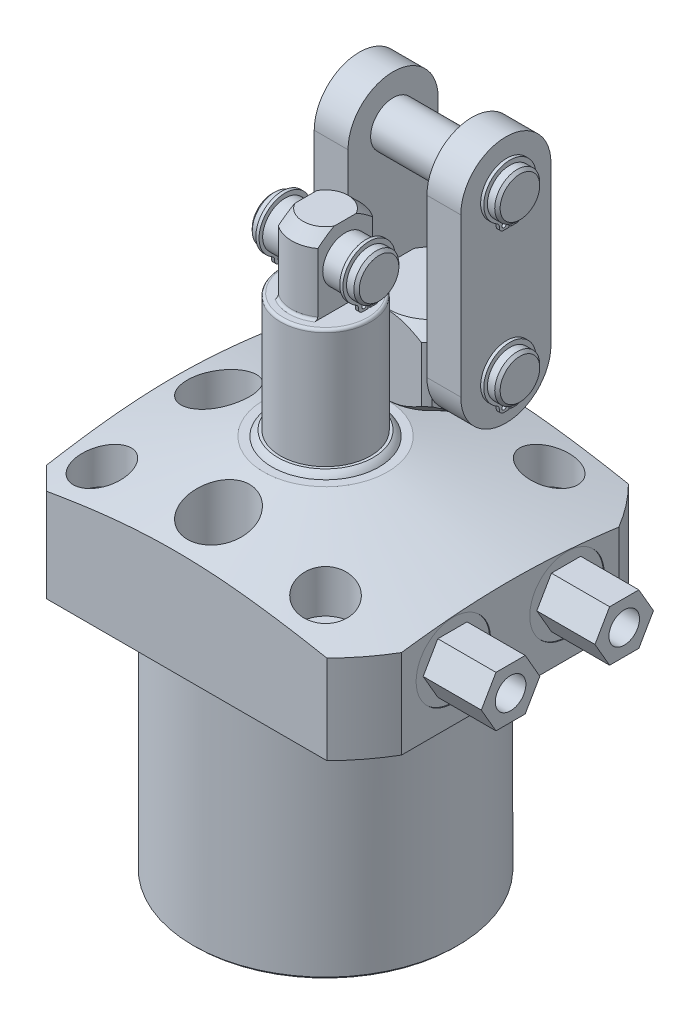
SolidWorks part; units mm, degrees
material "Alloy Steel"
ref_plane "Front Plane" through (0, 0, 0) normal (0, 0, 1) x (1, 0, 0)
ref_plane "Top Plane" through (0, 0, 0) normal (0, 1, 0) x (1, 0, 0)
ref_plane "Right Plane" through (0, 0, 0) normal (1, 0, 0) x (0, 0, -1)
sketch "Sketch28" plane through (0, 0, 0) normal (0, 0, 1) x (1, 0, 0)
  line L0 (0, 0) -> (0, 146.1857) construction
  line L1 (-17.4625, 36.4998) -> (-60.325, 25.0148)
  line L2 (-60.325, 25.0148) -> (-60.325, 0)
  line L3 (-60.325, 0) -> (-37.2999, 0)
  line L6 (-37.2999, 0) -> (-37.2999, -69.85)
  line L9 (-37.2999, -69.85) -> (0, -69.85)
  line L10 (0, -69.85) -> (0, 36.4998)
  line L11 (0, 36.4998) -> (-17.4625, 36.4998)
  dimension "D2" = 74.5998
  dimension "D3" = 69.85
  dimension "D5" = 120.65
  dimension "D6" = 15
  dimension "D7" = 34.925
  dimension "D8" = 36.4998
revolve "Revolve7" add sketch "Sketch28" angle 360 about L0
sketch "Sketch3" plane through (0, 36.4998, 0) normal (0, 1, 0) x (-1, 0, 0)
  line L0 (42.4688, -42.4688) -> (-51.9938, -42.4688)
  line L3 (-51.9938, 42.4688) -> (42.4688, 42.4688)
  line L4 (42.4688, -42.4688) -> (42.4688, 42.4688)
  line L5 (-51.9938, -42.4688) -> (-51.9938, 42.4688)
  line L6 (-29.7523, 0) -> (31.3525, 0) construction
  dimension "D1" = 84.9376
  dimension "D2" = 51.9938
  dimension "D5" = 42.4688
extrude "Cut-Extrude9" cut sketch "Sketch3" against normal up to next (106.3498 mm away) flip side to cut
chamfer "Chamfer8" distance 6.35 angle 45 2 edges at (-42.4688, 12.5429, -42.4688) (-42.4688, 12.5429, 42.4688)
chamfer "Chamfer5" distance 0.762 angle 45 1 edges at (0, -69.85, -37.2999)
hole_wizard "Hole1" positions "Sketch32" profile "Sketch31" legacy
sketch "Sketch32" plane through (0, 36.4998, 0) normal (0, 1, 0) x (-1, 0, 0)
  line L1 (0, 0) -> (-56.2722, 0) construction
  line L2 (0, 0) -> (0, 46.6984) construction
  point P11 (-31.496, -31.496)
  point P23 (-31.496, 31.496)
  point P25 (31.496, -31.496)
  point P26 (31.496, 31.496)
  dimension "D1" = 62.992
  dimension "D2" = 62.992
sketch "Sketch31" plane through (31.496, 36.4998, -31.496) normal (1, 0, 0) x (0, 0, 1)
  line L0 (0, 0) -> (0, 36.4998)
  line L1 (0, 36.4998) -> (4.3688, 36.4998)
  line L2 (4.3688, 36.4998) -> (4.3688, 17.4498)
  line L3 (4.3688, 17.4498) -> (7.1374, 17.4498)
  line L4 (7.1374, 17.4498) -> (7.1374, 0)
  line L5 (7.1374, 0) -> (0, 0)
  line L6 (0, 110) -> (0, -10) construction
  dimension "Diameter" = 8.7376
  dimension "Depth" = 36.4998
  dimension "C-Bore Diameter" = 14.2748
  dimension "C-Bore Depth" = 17.4498
sketch "Sketch34" plane through (0, 36.4998, 0) normal (0, 1, 0) x (1, 0, 0)
  line L0 (0, 0) -> (-28.6526, 0) construction
  circle A0 centre (0, 30.1498) radius 8.7503
  circle A1 centre (0, -30.1498) radius 8.7503
  circle A2 centre (0, 0) radius 30.1498 construction
  circle A3 centre (-30.1498, 0) radius 8.7503
  dimension "D1" = 17.5006
  dimension "D2" = 30.1498
extrude "Cut-Extrude10" cut sketch "Sketch34" against normal blind 19.05
ref_plane "Plane23" through (0, 15.875, 0) normal (0, -1, 0) x (1, 0, 0)
sketch "S2D0007" plane through (0, 15.875, 0) normal (0, -1, 0) x (1, 0, 0)
  line L0 (51.9938, -16.002) -> (51.9938, -26.4795)
  line L1 (51.9938, -26.4795) -> (51.7398, -26.4795)
  line L2 (51.7398, -26.4795) -> (51.7398, -22.2186)
  line L3 (51.7398, -22.2186) -> (49.6697, -21.7786)
  line L4 (49.6697, -21.7786) -> (48.8715, -20.9804)
  line L5 (48.8715, -20.9804) -> (37.7698, -20.9804)
  line L6 (37.7698, -20.9804) -> (34.7785, -16.002)
  line L7 (34.7785, -16.002) -> (51.9938, -16.002)
  line L8 (-11.7468, -16.002) -> (-12.1894, -16.002) construction
  line L10 (51.9938, -30.59) -> (51.9938, 30.59) construction
  dimension "D1" = 12.4333
  dimension "D2" = 59
  dimension "D3" = 9.9568
  dimension "D4" = 45
  dimension "D5" = 12
  dimension "D6" = 2.0701
  dimension "D7" = 0.254
  dimension "D8" = 20.955
  dimension "D9" = 16.002
  dimension "D10" = 13.97
revolve "Cut-Revolve2" cut sketch "S2D0007" angle 360 about L8
ref_plane "Plane24" through (0, 0, -16.002) normal (0, 0, 1) x (1, 0, 0)
sketch "Sketch6" plane through (0, 0, -16.002) normal (0, 0, 1) x (1, 0, 0)
  line L0 (42.8428, 0) -> (-36.1188, 0) construction
  line L1 (50.6793, 0) -> (50.6793, 1.4478)
  line L2 (50.6793, 1.4478) -> (47.6189, 1.4478)
  line L3 (42.8428, 0) -> (51.9938, 0) construction
  line L5 (45.0088, 0.5588) -> (46.1518, 0.5588)
  line L6 (45.0088, 0) -> (50.6793, 0)
  line L8 (45.0088, 0.5588) -> (45.0088, 0)
  line L9 (45.0088, -21.0492) -> (45.0088, 0.6686) construction
  arc A1 (46.1518, 0.5588) -> (47.6189, 1.4478) centre (45.0088, 4.1) ccw
  dimension "D8" = 3.7211
  dimension "D1" = 1.4478
  dimension "D2" = 45.0088
  dimension "D7" = 0.5588
  dimension "D9" = 11.3411
  dimension "D10" = 2.286
revolve "Cut-Revolve3" cut sketch "Sketch6" angle 360 about L9
sketch "Sketch38" plane through (51.7398, 0, 0) normal (1, 0, 0) x (0, 0, -1)
  line L1 (24.2436, 15.875) -> (20.1228, 23.0124)
  line L2 (20.1228, 23.0124) -> (11.8812, 23.0124)
  line L3 (11.8812, 23.0124) -> (7.7604, 15.875)
  line L4 (7.7604, 15.875) -> (11.8812, 8.7376)
  line L5 (11.8812, 8.7376) -> (20.1228, 8.7376)
  line L6 (20.1228, 8.7376) -> (24.2436, 15.875)
  circle A0 centre (16.002, 15.875) radius 7.1374 construction
  dimension "D1" = 14.2748
extrude "Extrude14" add sketch "Sketch38" along normal blind 16.383
hole_wizard "Hole2" positions "Sketch40" profile "Sketch39" legacy
sketch "Sketch40" plane through (68.1228, 0, 0) normal (1, 0, 0) x (0, 0, -1)
  circle A0 centre (16.002, 15.875) radius 10.4775 construction
  point P0 (16.002, 15.875)
sketch "Sketch39" plane through (68.1228, 15.875, -16.002) normal (0, 1, 0) x (0, 0, -1)
  line L0 (0, 0) -> (0, 6.7056)
  line L1 (0, 6.7056) -> (4.3053, 6.7056)
  line L2 (4.3053, 6.7056) -> (4.3053, 0)
  line L3 (4.3053, 0) -> (0, 0)
  line L4 (0, 110) -> (0, -10) construction
  dimension "Diameter" = 8.6106
  dimension "Depth" = 6.7056
mirror "Mirror6" about plane through (0, 0, 0) normal (0, 0, 1) of "Hole2", "Extrude14", "Cut-Revolve2", "Cut-Revolve3"
sketch "Sketch33" plane through (0, 0, -16.002) normal (0, 0, 1) x (1, 0, 0)
  line L0 (45.0088, 8.3297) -> (45.0088, -4.9597) construction
  line L1 (45.0088, 2.4904) -> (45.0088, -1.971) construction
  line L2 (39.3383, 1.4478) -> (50.6793, 1.4478) construction
  circle A0 centre (40.2272, 0.5842) radius 0.889
  dimension "D3" = 1.778
  dimension "D1" = 9.5631
  dimension "D2" = 0.8636
revolve "Revolve9" add sketch "Sketch33" angle 360 about L0
mirror "Mirror7" about plane through (0, 0, 0) normal (0, 0, 1) of bodies 147
sketch "Sketch12" plane through (0, 0, 0) normal (0, 0, -1) x (-1, 0, 0)
  line L0 (0, 36.4998) -> (0, 38.0238)
  line L1 (0, 38.0238) -> (13.462, 38.0238)
  line L2 (0, 36.4998) -> (15.0749, 36.4998)
  line L3 (0, 22.1056) -> (0, 27.6194) construction
  line L4 (17.4625, 36.4998) -> (-17.4625, 36.4998) construction
  arc A0 (15.0749, 36.4998) -> (13.462, 38.0238) centre (11.0966, 33.9049) ccw
  dimension "D1" = 4.7498
  dimension "D2" = 1.524
  dimension "D3" = 26.924
  dimension "D4" = 30.1498
revolve "Revolve2" add sketch "Sketch12" angle 360 about L3
ref_plane "Plane25" through (0, 0, 0) normal (-1, 0, 0) x (0, 0, 1)
sketch "Sketch13" plane through (0, 0, 0) normal (0, 0, 1) x (1, 0, 0)
  line L0 (0, 38.0238) -> (0, 92.075)
  line L1 (0, 92.075) -> (6.35, 92.075)
  line L2 (6.35, 92.075) -> (9.525, 88.9)
  line L3 (9.525, 71.4502) -> (9.525, 88.9)
  line L4 (12.6937, 38.0238) -> (0, 38.0238)
  line L5 (0, 23.0264) -> (0, 64.961) construction
  line L6 (-6.0362, 82.55) -> (17.7755, 82.55) construction
  line L7 (13.462, 38.0238) -> (-13.462, 38.0238) construction
  line L8 (42.8428, 0) -> (-36.1188, 0) construction
  line L10 (9.525, 71.4502) -> (12.6937, 71.4502)
  line L11 (12.6937, 71.4502) -> (12.6937, 38.0238)
  dimension "D1" = 9.525
  dimension "D2" = 82.55
  dimension "D3" = 19.05
  dimension "D4" = 45
  dimension "D5" = 3.175
  dimension "D6" = 25.3873
  dimension "D7" = 20.6248
revolve "Revolve3" add sketch "Sketch13" angle 360 about L5
sketch "Sketch14" plane through (0, 92.075, 0) normal (0, 1, 0) x (-1, 0, 0)
  line L0 (5.5499, 7.7411) -> (5.5499, -7.7411)
  line L2 (-5.5499, -7.7411) -> (-5.5499, 7.7411)
  line L4 (0, 0) -> (0, 0.0001) construction
  line L5 (0, -34.2265) -> (0, 34.2265) construction
  circle A0 centre (0, 0) radius 9.525 construction
  arc A1 (5.5499, -7.7411) -> (5.5499, 7.7411) centre (0, 0) ccw
  arc A2 (-5.5499, 7.7411) -> (-5.5499, -7.7411) centre (0, 0) ccw
  dimension "D1" = 11.0998
extrude "Cut-Extrude7" cut sketch "Sketch14" against normal up to surface (20.6248 mm away) up to face at (0, 71.4502, -9.525)
fillet "Fillet4" radius 0.762 3 edges at (0, 71.4502, -12.6937) (0, 71.4502, -9.525) (0, 71.4502, 9.525)
sketch "Sketch29" plane through (0, 0, 0) normal (-1, 0, 0) x (0, 0, 1)
  line L0 (-3.0856, 92.075) -> (-6.35, 92.075) construction
  circle A0 centre (0, 82.55) radius 6.3373
  dimension "D1" = 12.6746
  dimension "D2" = 9.525
extrude "Extrude11" add sketch "Sketch29" along normal mid plane 30.1498
sketch "Sketch16" plane through (-15.0749, 52.3748, 0) normal (-1, 0, 0) x (0, 0, 1)
  line L0 (0.2388, 24.2364) -> (0.2388, 21.4932)
  line L1 (2.982, 22.9316) -> (2.982, 22.687)
  line L2 (1.7882, 21.4932) -> (0.2388, 21.4932)
  line L3 (-2.982, 22.9316) -> (-2.982, 22.687)
  line L4 (-1.7882, 21.4932) -> (-0.2388, 21.4932)
  line L5 (-0.2388, 24.2364) -> (-0.2388, 21.4932)
  line L6 (0, -3.8062) -> (0, 3.1748) construction
  arc A0 (0.2388, 24.2364) -> (-0.2388, 24.2364) centre (0, 30.1752) ccw
  arc A1 (3.5934, 23.9737) -> (-3.5934, 23.9737) centre (0, 30.4038) ccw
  arc A2 (3.5934, 23.9737) -> (2.982, 22.9316) centre (4.1758, 22.9316) ccw
  arc A3 (1.7882, 21.4932) -> (2.982, 22.687) centre (1.7882, 22.687) ccw
  circle A4 centre (1.4326, 22.687) radius 0.5969
  arc A5 (-3.5934, 23.9737) -> (-2.982, 22.9316) centre (-4.1758, 22.9316) cw
  arc A6 (-1.7882, 21.4932) -> (-2.982, 22.687) centre (-1.7882, 22.687) cw
  circle A7 centre (-1.4326, 22.687) radius 0.5969
  circle A8 centre (0, 30.1752) radius 6.3373 construction
  dimension "D1" = 7.366
  dimension "D4" = 1.1938
  dimension "D6" = 1.1938
  dimension "D7" = 2.7432
  dimension "D8" = 5.9436
  dimension "D10" = 1.1938
  dimension "D11" = 1.1938
  dimension "D2" = 2.7432
  dimension "D3" = 0.2286
  dimension "D5" = 1.4326
  dimension "D9" = 0.4775
extrude "Extrude2" add sketch "Sketch16" against normal blind 0.889 from offset 2.8194
chamfer "Chamfer6" distance 0.762 angle 45 2 edges at (15.0749, 82.55, 6.3373) (-15.0749, 82.55, 6.3373)
mirror "Mirror2" about plane through (0, 0, 0) normal (-1, 0, 0) of "Extrude2"
sketch "Sketch35" plane through (0, 0, 0) normal (-1, 0, 0) x (0, 0, 1)
  line L0 (-30.1498, 43.5741) -> (-30.1498, 11.6793) construction
  line L1 (-30.1498, 17.4498) -> (-20.6248, 17.4498)
  line L2 (-20.6248, 17.4498) -> (-20.6248, 36.4998)
  line L3 (-20.6248, 36.4998) -> (-17.5768, 36.4998)
  line L4 (-14.2748, 39.8018) -> (-14.2748, 55.4228)
  line L5 (-17.5768, 58.7248) -> (-30.1498, 58.7248)
  line L6 (-30.1498, 58.7248) -> (-30.1498, 17.4498)
  line L8 (-14.2748, 55.4228) -> (-17.5768, 58.7248)
  line L9 (-17.5768, 36.4998) -> (-14.2748, 39.8018)
  line L10 (30.59, 0) -> (42.4688, 0) construction
  point P6 (-14.2748, 36.4998)
  point P7 (-14.2748, 58.7248)
  dimension "D2" = 19.05
  dimension "D3" = 31.75
  dimension "D4" = 41.275
  dimension "D5" = 22.225
  dimension "D6" = 30.1498
  dimension "D9" = 3.302
  dimension "D10" = 3.302
  dimension "D7" = 36.4998
revolve "Revolve10" add sketch "Sketch35" angle 360 about L0
sketch "Sketch36" plane through (0, 58.7248, 0) normal (0, 1, 0) x (1, 0, 0)
  line L0 (0, 30.1498) -> (-30.1498, 30.1498) construction
  line L1 (11.1125, 41.4868) -> (11.1125, 18.8128)
  line L2 (9.525, 42.8498) -> (-9.525, 42.8498)
  line L3 (-11.1125, 41.4868) -> (-11.1125, 18.8128)
  line L4 (9.525, 17.4498) -> (-9.525, 17.4498)
  line L5 (0, 30.1498) -> (0, 0) construction
  line L6 (0, 34.2265) -> (0, -34.2265) construction
  circle A0 centre (0, 30.1498) radius 15.875 construction
  arc A2 (9.525, 42.8498) -> (-9.525, 42.8498) centre (0, 30.1498) ccw
  arc A3 (-11.1125, 41.4868) -> (-11.1125, 18.8128) centre (0, 30.1498) ccw
  arc A4 (11.1125, 18.8128) -> (11.1125, 41.4868) centre (0, 30.1498) ccw
  arc A5 (-9.525, 17.4498) -> (9.525, 17.4498) centre (0, 30.1498) ccw
  dimension "D1" = 25.4
  dimension "D2" = 22.225
extrude "Cut-Extrude11" cut sketch "Sketch36" against normal up to surface (22.225 mm away) up to face at (0, 36.4998, -17.5768)
sketch "Sketch30" plane through (0, 0, 0) normal (-1, 0, 0) x (0, 0, 1)
  line L0 (-42.4688, 0) -> (42.4688, 0) construction
  circle A0 centre (-30.1498, 47.625) radius 6.3373
  dimension "D3" = 12.6746
  dimension "D1" = 47.625
  dimension "D2" = 30.1498
extrude "Extrude12" add sketch "Sketch30" along normal mid plane 49.1998
sketch "Sketch19" plane through (-24.5999, 11.0998, -22.225) normal (-1, 0, 0) x (0, 0, 1)
  line L0 (-7.686, 30.5864) -> (-7.686, 27.8432)
  line L1 (-4.9428, 29.2816) -> (-4.9428, 29.037)
  line L2 (-6.1366, 27.8432) -> (-7.686, 27.8432)
  line L3 (-10.9068, 29.2816) -> (-10.9068, 29.037)
  line L4 (-9.713, 27.8432) -> (-8.1636, 27.8432)
  line L5 (-8.1636, 30.5864) -> (-8.1636, 27.8432)
  line L6 (-7.9248, -5.3833) -> (-7.9248, 4.2478) construction
  arc A0 (-7.686, 30.5864) -> (-8.1636, 30.5864) centre (-7.9248, 36.5252) ccw
  arc A1 (-4.3314, 30.3237) -> (-11.5182, 30.3237) centre (-7.9248, 36.7538) ccw
  arc A2 (-4.3314, 30.3237) -> (-4.9428, 29.2816) centre (-3.749, 29.2816) ccw
  arc A3 (-6.1366, 27.8432) -> (-4.9428, 29.037) centre (-6.1366, 29.037) ccw
  circle A4 centre (-6.2535, 29.037) radius 0.5969
  arc A5 (-11.5182, 30.3237) -> (-10.9068, 29.2816) centre (-12.1006, 29.2816) cw
  arc A6 (-9.713, 27.8432) -> (-10.9068, 29.037) centre (-9.713, 29.037) cw
  circle A7 centre (-9.5961, 29.037) radius 0.5969
  circle A8 centre (-7.9248, 36.5252) radius 6.3373 construction
  dimension "D1" = 7.366
  dimension "D3" = 0.2286
  dimension "D4" = 1.1938
  dimension "D5" = 1.1938
  dimension "D6" = 1.1938
  dimension "D9" = 5.9436
  dimension "D2" = 2.7432
  dimension "D7" = 0.4775
  dimension "D8" = 2.7432
  dimension "D10" = 1.1938
  dimension "D11" = 1.4326
extrude "Extrude4" add sketch "Sketch19" against normal blind 0.889 from offset 2.8194
sketch "Sketch37" plane through (-11.1125, 0, 0) normal (-1, 0, 0) x (0, 0, 1)
  line L0 (-42.8498, 92.075) -> (-42.8498, 47.625)
  line L1 (-17.4498, 92.075) -> (-17.4498, 47.625)
  arc A0 (-17.4498, 92.075) -> (-42.8498, 92.075) centre (-30.1498, 92.075) ccw
  arc A1 (-42.8498, 47.625) -> (-17.4498, 47.625) centre (-30.1498, 47.625) ccw
  dimension "D1" = 25.4
  dimension "D2" = 44.45
  dimension "D3" = 31.6186
extrude "Extrude13" add sketch "Sketch37" along normal blind 9.525
mirror "Mirror3" about plane through (0, 0, 0) normal (-1, 0, 0) of "Extrude4"
chamfer "Chamfer7" distance 0.762 angle 45 2 edges at (24.5999, 47.625, -23.8125) (-24.5999, 47.625, -23.8125)
pattern_linear "LPattern2" count 2 spacing 44.45 along (0, 1, 0) of "Extrude4", "Mirror3", "Chamfer7", "Extrude12"
mirror "Mirror8" about plane through (0, 0, 0) normal (-1, 0, 0) of "Extrude13"
